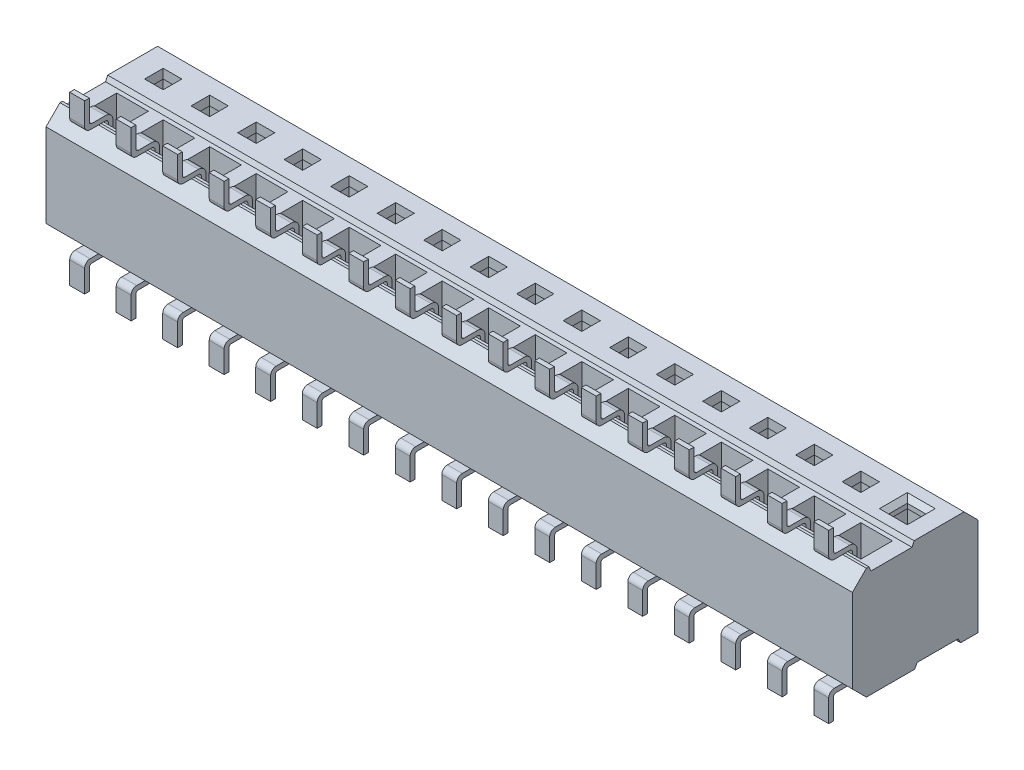
SolidWorks part; units mm, degrees
ref_plane "Front" through (0, 0, 0) normal (0, 0, 1) x (1, 0, 0)
ref_plane "Top" through (0, 0, 0) normal (0, 1, 0) x (1, 0, 0)
ref_plane "Right" through (0, 0, 0) normal (1, 0, 0) x (0, 0, -1)
sketch "Sketch1" plane through (0, 0, 0) normal (0, 1, 0) x (1, 0, 0)
  line L0 (-11.0109, -1.7145) -> (11.0109, 1.7145) construction
  line L1 (-11.0109, 1.7145) -> (11.0109, 1.7145)
  line L2 (-11.0109, 1.7145) -> (-11.0109, -1.7145)
  line L3 (-11.0109, -1.7145) -> (11.0109, -1.7145)
  line L4 (11.0109, 1.7145) -> (11.0109, -1.7145)
  dimension "D1" = 3.429
  dimension "D2" = 22.0218
extrude "Main Body" add sketch "Sketch1" along normal blind 3.048
ref_plane "Plane2" through (10.16, 0, 0) normal (1, 0, 0) x (0, 0, -1)
sketch "Sketch2" plane through (0, 3.048, 0) normal (0, 1, 0) x (-1, 0, 0)
  line L0 (0, 0) -> (-9.2157, 0) construction
  line L1 (-6.4241, -0.635) -> (-4.2326, -0.635) construction
  line L2 (-10.414, -0.381) -> (-9.906, -0.381)
  line L3 (-10.414, -0.381) -> (-10.414, -0.889)
  line L4 (-10.414, -0.889) -> (-9.906, -0.889)
  line L6 (-9.906, -0.381) -> (-9.906, -0.889)
  line L7 (-9.906, 0.381) -> (-9.906, 0.889)
  line L8 (-10.414, 0.889) -> (-9.906, 0.889)
  line L9 (-10.414, 0.381) -> (-10.414, 0.889)
  line L10 (-10.16, 1.9747) -> (-10.16, -2.1621) construction
  line L11 (-11.0109, 1.7145) -> (-11.0109, -1.7145) construction
  line L12 (-10.414, 0.381) -> (-9.906, 0.381)
  line L13 (-6.4241, 0.635) -> (-4.3872, 0.635) construction
  dimension "D1" = 1.27
  dimension "D2" = 0.508
  dimension "D3" = 0.508
  dimension "D4" = 0.8509
extrude "Cut-Extrude1" cut sketch "Sketch2" against normal blind 2.794
chamfer "Chamfer1" distance 0.127 distance2 0.127 8 edges at (10.414, 3.048, -0.635) (10.16, 3.048, -0.889) (9.906, 3.048, -0.635) (10.16, 3.048, -0.381) (10.16, 3.048, 0.381) (9.906, 3.048, 0.635) (10.16, 3.048, 0.889) (10.414, 3.048, 0.635)
sketch "Sketch6" plane through (11.0109, 0, 0) normal (1, 0, 0) x (0, 0, -1)
  line L1 (-1.7145, 3.048) -> (-1.7145, 0) construction
  line L2 (-1.7145, 0) -> (1.7145, 0) construction
  line L3 (-1.4097, 0) -> (1.4097, 0)
  line L5 (-1.4097, 0.127) -> (-1.4097, 0)
  line L7 (-1.4097, 0.127) -> (1.4097, 0.127)
  line L9 (1.4097, 0.127) -> (1.4097, 0)
  line L12 (1.7145, 3.048) -> (1.7145, 0) construction
  dimension "D2" = 0.3048
  dimension "D1" = 0.127
  dimension "D3" = 0.3048
sketch "Sketch7" plane through (10.16, 0, 0) normal (1, 0, 0) x (0, 0, -1)
  line L0 (0, 0) -> (0, 2.2434) construction
  line L1 (-0.889, 1.5621) -> (-0.889, 1.0541)
  line L2 (-1.143, 0.9271) -> (-2.159, 0.9271)
  line L3 (-0.889, 0.254) -> (-0.889, 2.921) construction
  line L4 (-1.016, 1.5621) -> (-1.016, 1.0541)
  line L5 (-2.159, 0.9271) -> (-2.159, 0.8001)
  line L6 (-1.143, 0.8001) -> (-2.159, 0.8001)
  line L7 (-1.7145, 3.048) -> (1.7145, 3.048) construction
  line L8 (-1.016, 1.5621) -> (-0.889, 1.5621)
  line L9 (1.016, 1.5621) -> (0.889, 1.5621)
  line L10 (1.143, 0.8001) -> (2.159, 0.8001)
  line L11 (2.159, 0.9271) -> (2.159, 0.8001)
  line L12 (1.016, 1.5621) -> (1.016, 1.0541)
  line L13 (1.143, 0.9271) -> (2.159, 0.9271)
  line L14 (0.889, 1.5621) -> (0.889, 1.0541)
  arc A0 (-0.889, 1.0541) -> (-1.143, 0.8001) centre (-1.143, 1.0541) cw
  arc A1 (-1.016, 1.0541) -> (-1.143, 0.9271) centre (-1.143, 1.0541) cw
  arc A2 (1.016, 1.0541) -> (1.143, 0.9271) centre (1.143, 1.0541) ccw
  arc A3 (0.889, 1.0541) -> (1.143, 0.8001) centre (1.143, 1.0541) ccw
  dimension "D2" = 0.254
  dimension "D1" = 2.2479
  dimension "D4" = 4.318
  dimension "D5" = 0.762
  dimension "D3" = 0.127
sketch "Sketch30" plane through (10.16, 0, 0) normal (1, 0, 0) x (0, 0, -1)
  line L0 (-1.7145, 3.048) -> (1.7145, 3.048) construction
  line L1 (-1.0668, 3.048) -> (-0.2032, 3.048)
  line L2 (-1.0668, 3.048) -> (-1.0668, 0.254)
  line L3 (-1.0668, 0.254) -> (-0.2032, 0.254)
  line L4 (-0.2032, 3.048) -> (-0.2032, 0.254)
  line L5 (-1.7145, 0) -> (1.7145, 0) construction
  line L6 (0.2032, 0) -> (1.0668, 0)
  line L7 (0.2032, 0) -> (0.2032, 2.794)
  line L8 (0.2032, 2.794) -> (1.0668, 2.794)
  line L9 (1.0668, 0) -> (1.0668, 2.794)
  line L10 (-0.635, 0.254) -> (-0.635, 1.4535) construction
  line L12 (0.635, 2.794) -> (0.635, 2.0625) construction
  line L14 (0, 0) -> (0, 3.8542) construction
  point P14 (0, 0)
  dimension "D1" = 0.254
  dimension "D3" = 0.8636
  dimension "D4" = 1.27
  dimension "D5" = 0.8636
  dimension "D6" = 0.254
extrude "Pin Cut-DH" cut sketch "Sketch30" against normal mid plane 0.8636
sketch "Sketch10" plane through (11.0109, 0, 0) normal (1, 0, 0) x (0, 0, -1)
  line L0 (0, 3.5147) -> (0, -0.2313) construction
  line L1 (-1.7373, 1.524) -> (1.6711, 1.524) construction
  line L2 (-1.7145, 3.048) -> (-1.3335, 3.048)
  line L3 (-1.7145, 3.048) -> (1.7145, 3.048) construction
  line L4 (-1.2649, 3.048) -> (-0.0305, 3.048)
  line L5 (-1.7145, 3.048) -> (-1.7145, 2.667)
  line L6 (-1.7145, 2.667) -> (-1.3335, 3.048)
  line L7 (1.7145, 2.667) -> (1.3335, 3.048)
  line L8 (-1.7145, 0) -> (1.7145, 0) construction
  line L9 (1.7145, 3.048) -> (1.7145, 2.667)
  line L10 (1.7145, 3.048) -> (1.3335, 3.048)
  line L11 (-1.7145, 0.381) -> (-1.3335, 0)
  line L12 (-1.7145, 0) -> (-1.7145, 0.381)
  line L13 (-1.7145, 0) -> (-1.3335, 0)
  line L14 (-0.0305, 3.048) -> (-0.0889, 2.921)
  line L15 (-0.0889, 2.921) -> (-1.2065, 2.921)
  line L16 (-1.2065, 2.921) -> (-1.2649, 3.048)
  line L17 (-0.0152, 0) -> (0.0533, 0.127)
  line L18 (0.0533, 0.127) -> (1.1709, 0.127)
  line L19 (1.1709, 0.127) -> (1.2395, 0)
  line L20 (-0.0152, 0) -> (1.2395, 0)
  line L21 (-0.6477, 2.921) -> (-0.6477, 2.4488) construction
  line L22 (1.7145, 3.048) -> (1.7145, 0) construction
  line L23 (0.6121, 0.127) -> (0.6121, 0.4568) construction
  dimension "D2" = 0.381
  dimension "D3" = 0.0686
  dimension "D1" = 0.381
  dimension "D4" = 0.127
  dimension "D5" = 0.0584
  dimension "D6" = 1.1176
  dimension "D7" = 0.127
  dimension "D8" = 1.1176
  dimension "D9" = 0.0686
  dimension "D10" = 0.475
extrude "Body Cut-DH" cut sketch "Sketch10" against normal through all
pattern_linear "DH Cut Pattern" count 17 spacing 1.27 along (-1, 0, 0) of "Cut-Extrude1", "Pin Cut-DH"
sketch "Sketch11" plane through (10.16, 0, 0) normal (1, 0, 0) x (0, 0, -1)
  line L0 (-0.0305, 3.048) -> (1.3335, 3.048) construction
  line L1 (-1.0668, 2.921) -> (-1.0668, 0.254) construction
  line L2 (-1.5621, 3.048) -> (-1.143, 3.048)
  line L3 (-1.7145, 2.667) -> (-1.7145, 0.381) construction
  line L4 (-1.7145, 3.81) -> (-1.7145, 3.2004)
  line L5 (-1.0668, 2.9718) -> (-1.0668, 2.4867)
  line L6 (-1.3335, 0) -> (-0.0152, 0) construction
  line L8 (-0.9398, 2.9718) -> (-0.9398, 2.4867)
  line L9 (-1.5113, 3.175) -> (-1.143, 3.175)
  line L10 (-1.5875, 3.81) -> (-1.5875, 3.2512)
  line L11 (-1.0668, 2.4867) -> (-0.9398, 2.4867)
  line L12 (-1.7145, 3.81) -> (-1.5875, 3.81)
  line L13 (0.2032, 0.6865) -> (0.2032, 0.0762)
  line L15 (-1.5621, 0) -> (0.127, 0)
  line L16 (-1.5875, -0.2032) -> (-1.5875, -0.762)
  line L17 (-1.7145, -0.1524) -> (-1.7145, -0.762)
  line L18 (0.3302, 0.6865) -> (0.3302, 0.0762)
  line L19 (-1.5113, -0.127) -> (0.127, -0.127)
  line L20 (-1.7145, -0.762) -> (-1.5875, -0.762)
  line L21 (0.2032, 0.6865) -> (0.3302, 0.6865)
  line L24 (0.2032, 2.794) -> (0.2032, 0.127) construction
  arc A0 (-1.0668, 2.9718) -> (-1.143, 3.048) centre (-1.143, 2.9718) ccw
  arc A1 (-1.5621, 3.048) -> (-1.7145, 3.2004) centre (-1.5621, 3.2004) cw
  arc A2 (-0.9398, 2.9718) -> (-1.143, 3.175) centre (-1.143, 2.9718) ccw
  arc A3 (-1.5621, 0) -> (-1.7145, -0.1524) centre (-1.5621, -0.1524) ccw
  arc A4 (0.2032, 0.0762) -> (0.127, 0) centre (0.127, 0.0762) cw
  arc A5 (0.3302, 0.0762) -> (0.127, -0.127) centre (0.127, 0.0762) cw
  arc A6 (-1.5113, -0.127) -> (-1.5875, -0.2032) centre (-1.5113, -0.2032) ccw
  arc A7 (-1.5113, 3.175) -> (-1.5875, 3.2512) centre (-1.5113, 3.2512) cw
  dimension "D1" = 0.0762
  dimension "D5" = 0.762
  dimension "D8" = 0.1524
  dimension "D7" = 0.0762
  dimension "D9" = 0.0762
  dimension "D12" = 0.2032
  dimension "D13" = 0.0762
  dimension "D14" = 0.1524
  dimension "D3" = 0.127
  dimension "D4" = 0.127
  dimension "D10" = 0.762
  dimension "D11" = 0.8135
  dimension "D15" = 0.6883
  dimension "D6" = 0.127
extrude "Lead Pin-DH" add sketch "Sketch11" along normal mid plane 0.4064
pattern_linear "Lead Pattern-DH" count 17 spacing 1.27 along (-1, 0, 0) of "Lead Pin-DH"
